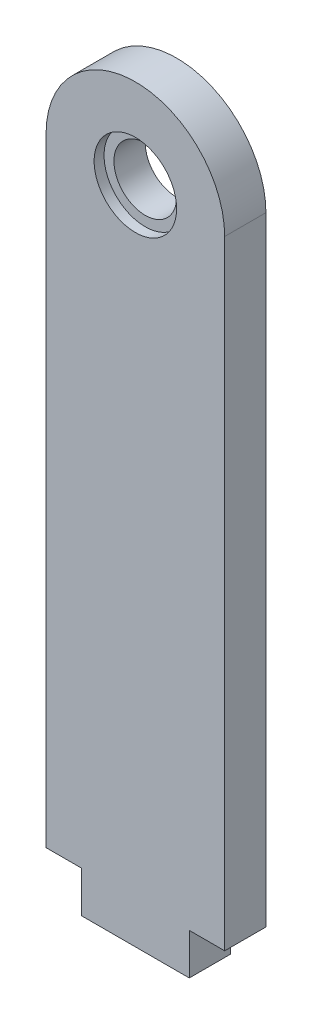
SolidWorks part; units mm, degrees
ref_plane "Front Plane" through (0, 0, 0) normal (0, 0, 1) x (1, 0, 0)
ref_plane "Top Plane" through (0, 0, 0) normal (0, 1, 0) x (1, 0, 0)
ref_plane "Right Plane" through (0, 0, 0) normal (1, 0, 0) x (0, 0, -1)
sketch "Sketch1" plane through (0, 0, 0) normal (0, 0, 1) x (1, 0, 0)
  line L1 (0, 0) -> (27.5, 0)
  line L2 (0, 0) -> (0, 95.25)
  line L3 (0, 95.25) -> (27.5, 95.25)
  line L4 (27.5, 0) -> (27.5, 95.25)
  line L5 (5.4495, 0) -> (22.0505, 0)
  line L6 (5.4495, 0) -> (5.4495, -6.35)
  line L7 (5.4495, -6.35) -> (22.0505, -6.35)
  line L8 (22.0505, 0) -> (22.0505, -6.35)
  arc A0 (0, 95.25) -> (27.5, 95.25) centre (13.75, 95.25) cw
  circle A1 centre (13.75, 95.25) radius 4.826
  circle A2 centre (13.75, 95.25) radius 6.35
  point P12 (13.75, 0)
  point P13 (13.75, 0)
  dimension "D1" = 9.652
  dimension "D2" = 12.7
  dimension "D3" = 6.35
  dimension "D4" = 101.6
  dimension "D5" = 27.5
extrude "Boss-Extrude1" add sketch "Sketch1" along normal blind 6.35 contours A2 L3 L2 L1 L4 | L3 A2 A1 | L3 A2 A1 | A2 L3 A0 | L8 L1 L6 L7
sketch "Sketch2" plane through (0, 0, 6.35) normal (0, 0, 1) x (1, 0, 0)
  line L7 (0, 95.25) -> (0, 0)
  line L8 (0, 0) -> (5.4495, 0)
  line L9 (5.4495, 0) -> (5.4495, -6.35)
  line L10 (5.4495, -6.35) -> (22.0505, -6.35)
  line L11 (22.0505, -6.35) -> (22.0505, 0)
  line L12 (22.0505, 0) -> (27.5, 0)
  line L13 (27.5, 0) -> (27.5, 95.25)
  line L14 (0, 95.25) -> (0, 0)
  line L15 (0, 0) -> (5.4495, 0)
  line L16 (5.4495, 0) -> (5.4495, -6.35)
  line L17 (5.4495, -6.35) -> (22.0505, -6.35)
  line L18 (22.0505, -6.35) -> (22.0505, 0)
  line L19 (22.0505, 0) -> (27.5, 0)
  line L20 (27.5, 0) -> (27.5, 95.25)
  circle A0 centre (13.75, 95.25) radius 4.826 construction
  arc A1 (27.5, 95.25) -> (0, 95.25) centre (13.75, 95.25) ccw
  arc A2 (27.5, 95.25) -> (0, 95.25) centre (13.75, 95.25) ccw
  circle A3 centre (13.75, 95.25) radius 4.826
  circle A4 centre (13.75, 95.25) radius 6.35
  circle M9 centre (13.75, 95.25) radius 4.826
  dimension "D2" = 12.7
  dimension "D1" = 0
extrude "Cut-Extrude1" cut sketch "Sketch2" against normal blind 1.524 contours A4 M9
